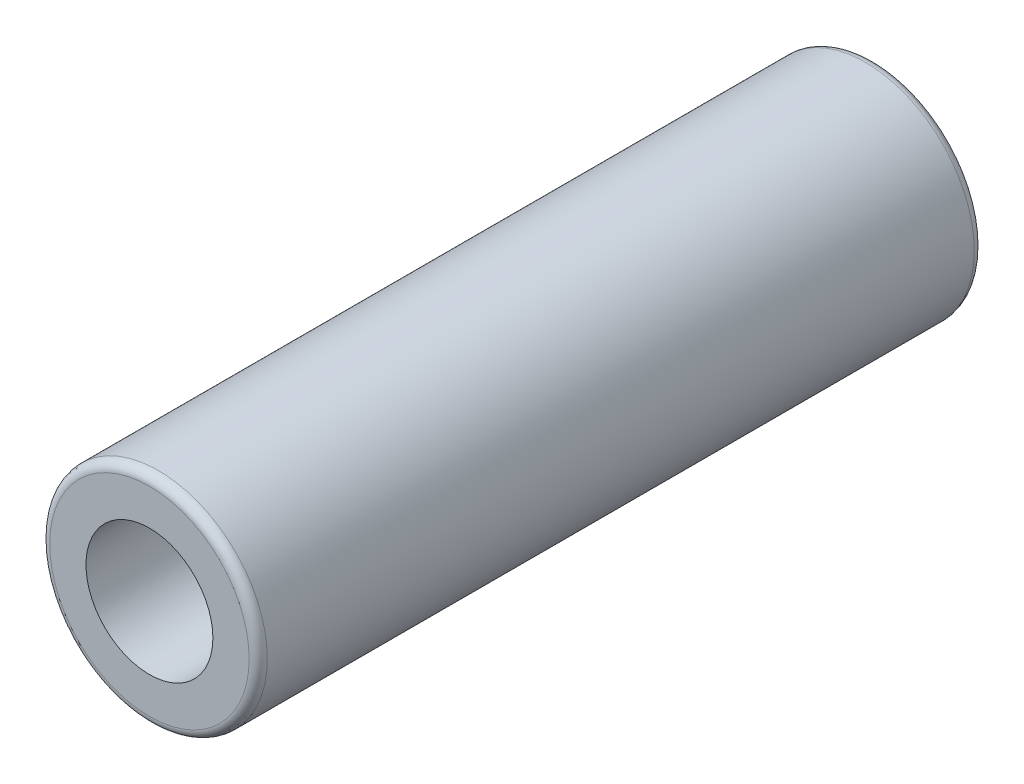
SolidWorks part; units mm, degrees
ref_plane "Front Plane" through (0, 0, 0) normal (0, 0, 1) x (1, 0, 0)
ref_plane "Top Plane" through (0, 0, 0) normal (0, 1, 0) x (1, 0, 0)
ref_plane "Right Plane" through (0, 0, 0) normal (1, 0, 0) x (0, 0, -1)
sketch "Sketch1" plane through (0, 0, 0) normal (0, 0, 1) x (1, 0, 0)
  circle A0 centre (0, 0) radius 3.5
  circle A1 centre (0, 0) radius 6
  dimension "D1" = 7
  dimension "D2" = 12
extrude "Boss-Extrude1" add sketch "Sketch1" along normal blind 40
fillet "Fillet1" radius 0.5 1 edges at (6, 0, 40)
fillet "Fillet2" radius 0.5 1 edges at (6, 0, 0)
